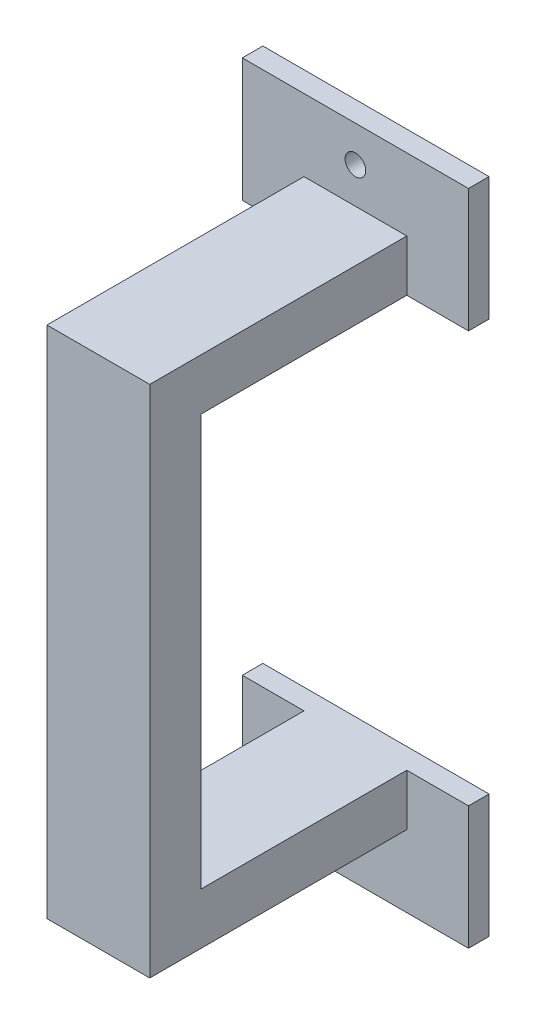
SolidWorks part; units mm, degrees
ref_plane "Front Plane" through (0, 0, 0) normal (0, 0, 1) x (1, 0, 0)
ref_plane "Top Plane" through (0, 0, 0) normal (0, 1, 0) x (1, 0, 0)
ref_plane "Right Plane" through (0, 0, 0) normal (1, 0, 0) x (0, 0, -1)
sketch "Sketch2" plane through (0, 0, 0) normal (1, 0, 0) x (0, 0, -1)
  line L0 (0, 44.0961) -> (0, -19.4039) construction
  line L9 (0, 44.0961) -> (-31.75, 44.0961)
  line L10 (-31.75, 44.0961) -> (-31.75, -19.4039)
  line L11 (-31.75, -19.4039) -> (0, -19.4039)
  line L12 (0, -19.4039) -> (0, -13.0539)
  line L13 (0, -13.0539) -> (-25.4, -13.0539)
  line L14 (-25.4, -13.0539) -> (-25.4, 37.7461)
  line L15 (-25.4, 37.7461) -> (0, 37.7461)
  line L16 (0, 37.7461) -> (0, 44.0961)
  dimension "D1" = 6.35
  dimension "D2" = 6.35
  dimension "D3" = 6.35
  dimension "D4" = 63.5
  dimension "D5" = 25.4
  dimension "D6" = 44.0961
extrude "Boss-Extrude1" add sketch "Sketch2" along normal blind 12.7
sketch "Sketch3" plane through (0, 0, 0) normal (0, 0, -1) x (-1, 0, 0)
  line L0 (-6.35, 44.0961) -> (-6.35, 52.9861) construction
  line L2 (-12.7, 37.7461) -> (0, 37.7461) construction
  line L3 (-20.32, 52.9861) -> (-20.32, 37.7461)
  line L4 (-20.32, 52.9861) -> (7.62, 52.9861)
  line L5 (-20.32, 37.7461) -> (7.62, 37.7461)
  line L6 (7.62, 52.9861) -> (7.62, 37.7461)
  line L7 (0, 37.7461) -> (0, 44.0961) construction
  line L8 (-12.7, 37.7461) -> (-12.7, 44.0961) construction
  line L10 (-12.7, 44.0961) -> (0, 44.0961) construction
  line L11 (-12.7, 12.3461) -> (0, 12.3461) construction
  line L16 (-20.32, -28.2939) -> (-20.32, -13.0539)
  line L17 (-20.32, -28.2939) -> (7.62, -28.2939)
  line L18 (7.62, -28.2939) -> (7.62, -13.0539)
  line L19 (-20.32, -13.0539) -> (7.62, -13.0539)
  circle A0 centre (-6.35, 48.5411) radius 1.27
  circle A2 centre (-6.35, -23.8489) radius 1.27
  point P25 (0, 12.3461)
  point P26 (-12.7, 12.3461)
  point P27 (0, 12.3461)
  dimension "D1" = 2.54
  dimension "D5" = 4.445
  dimension "D7" = 13.97
  dimension "D2" = 0
  dimension "D3" = 7.62
  dimension "D4" = 7.62
  dimension "D6" = 8.89
  dimension "D8" = 25.4
extrude "Boss-Extrude2" add sketch "Sketch3" along normal blind 2.54
